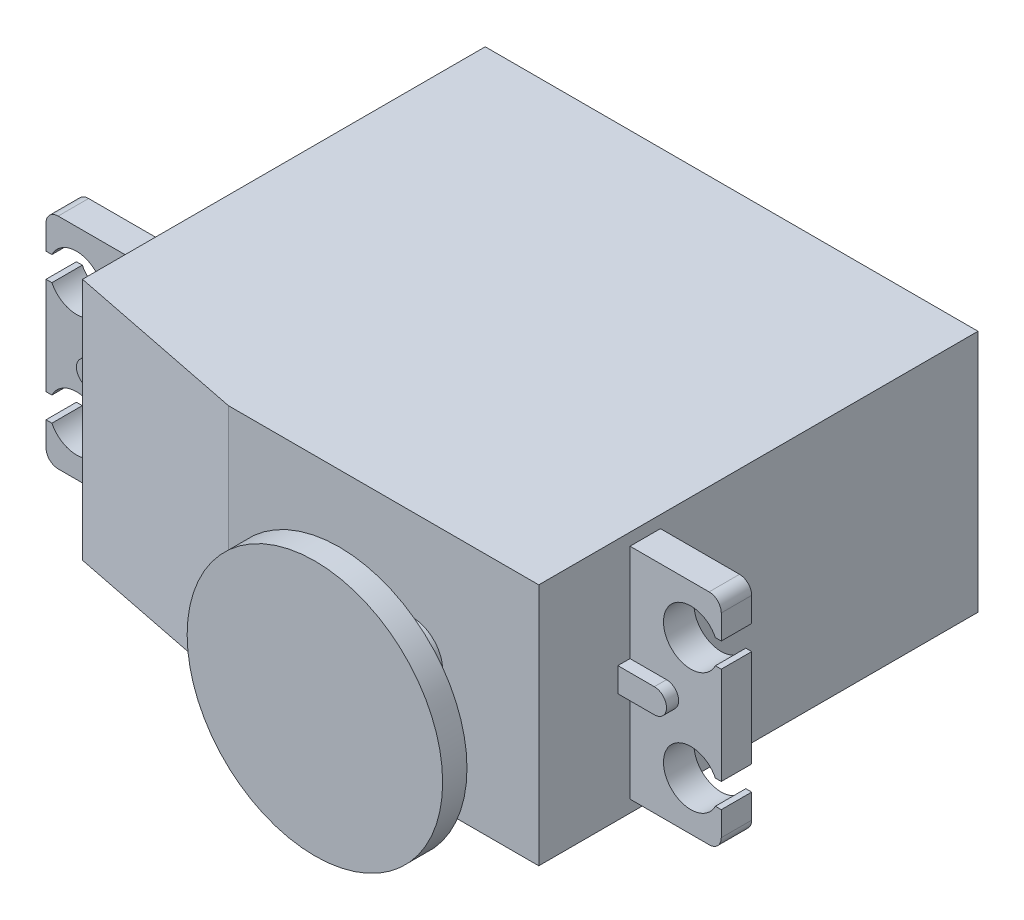
SolidWorks part; units mm, degrees
ref_plane "Front Plane" through (0, 0, 0) normal (0, 0, 1) x (1, 0, 0)
ref_plane "Top Plane" through (0, 0, 0) normal (0, 1, 0) x (1, 0, 0)
ref_plane "Right Plane" through (0, 0, 0) normal (1, 0, 0) x (0, 0, -1)
sketch "Sketch1" plane through (0, 0, 0) normal (0, 0, 1) x (1, 0, 0)
  line L1 (-20.25, 10) -> (20.25, 10)
  line L2 (-20.25, 10) -> (-20.25, -10)
  line L3 (-20.25, -10) -> (20.25, -10)
  line L4 (20.25, 10) -> (20.25, -10)
  line L5 (-20.25, 10) -> (20.25, -10) construction
  line L6 (-20.25, -10) -> (20.25, 10) construction
  point P0 (0, 0)
  dimension "D1" = 20
  dimension "D2" = 40.5
extrude "Boss-Extrude1" add sketch "Sketch1" along normal blind 36.1
ref_plane "Plane1" through (0, 0, 26.1) normal (0, 0, -1) x (-1, 0, 0)
sketch "Sketch2" plane through (0, 0, 26.1) normal (0, 0, -1) x (-1, 0, 0)
  line L0 (-20.25, -10) -> (-20.25, 10) construction
  line L1 (-20.25, 9) -> (-27.75, 9)
  line L2 (-20.25, 9) -> (-20.25, -9)
  line L3 (-20.25, -9) -> (-27.75, -9)
  line L4 (-27.75, 9) -> (-27.75, 6)
  line L5 (-20.25, 10) -> (20.25, 10) construction
  line L6 (-27.75, 4) -> (-27.75, -4)
  line L7 (-27.75, 6) -> (-27.2656, 6)
  line L8 (-27.75, -6) -> (-27.75, -9)
  line L9 (-27.75, 4) -> (-27.2656, 4)
  line L10 (-27.75, -4) -> (-27.2656, -4)
  line L12 (-27.75, -6) -> (-27.2656, -6)
  arc A0 (-27.2656, 4) -> (-27.2656, 6) centre (-25.25, 5) ccw
  arc A1 (-27.2656, -6) -> (-27.2656, -4) centre (-25.25, -5) ccw
  dimension "D4" = 4.5
  dimension "D7" = 25.25
  dimension "D1" = 18
  dimension "D2" = 1
  dimension "D3" = 7.5
  dimension "D5" = 10
  dimension "D6" = 5
  dimension "D8" = 2
  dimension "D9" = 1
  dimension "D10" = 2
  dimension "D11" = 1
extrude "Boss-Extrude2" add sketch "Sketch2" against normal blind 2.5
sketch "Sketch3" plane through (0, 0, 28.6) normal (0, 0, 1) x (1, 0, 0)
  line L0 (20.25, 0) -> (23.25, 0) construction
  line L1 (20.25, -10) -> (20.25, 10) construction
  line L2 (20.25, 1) -> (23.25, 1)
  line L3 (20.25, -1) -> (23.25, -1)
  line L4 (20.25, -9) -> (20.25, 9) construction
  line L5 (20.25, 1) -> (20.25, -1)
  arc A1 (23.25, -1) -> (23.25, 1) centre (23.25, 0) ccw
  dimension "D1" = 1
  dimension "D2" = 3
  dimension "D3" = 1
  dimension "D4" = 2
extrude "Boss-Extrude3" add sketch "Sketch3" along normal blind 1
fillet "Fillet1" radius 1 2 edges at (27.75, -9, 27.35) (27.75, 9, 27.35)
mirror "Mirror1" about plane through (0, 0, 0) normal (1, 0, 0) of "Fillet1", "Boss-Extrude3", "Boss-Extrude2"
chamfer "Chamfer1" distance 3 distance2 15 1 edges at (-20.25, 0, 36.1)
sketch "Sketch4" plane through (0, 0, 36.1) normal (0, 0, 1) x (1, 0, 0)
  line L0 (-20.25, 1) -> (-20.25, 9) construction
  circle A0 centre (9.85, 0) radius 2.5
  dimension "D1" = 5
  dimension "D2" = 30.1
extrude "Boss-Extrude4" add sketch "Sketch4" along normal blind 6
sketch "Sketch5" plane through (0, 0, 42.1) normal (0, 0, 1) x (1, 0, 0)
  circle A0 centre (9.85, 0) radius 10.5
  dimension "D1" = 21
extrude "Boss-Extrude5" add sketch "Sketch5" along normal blind 2
